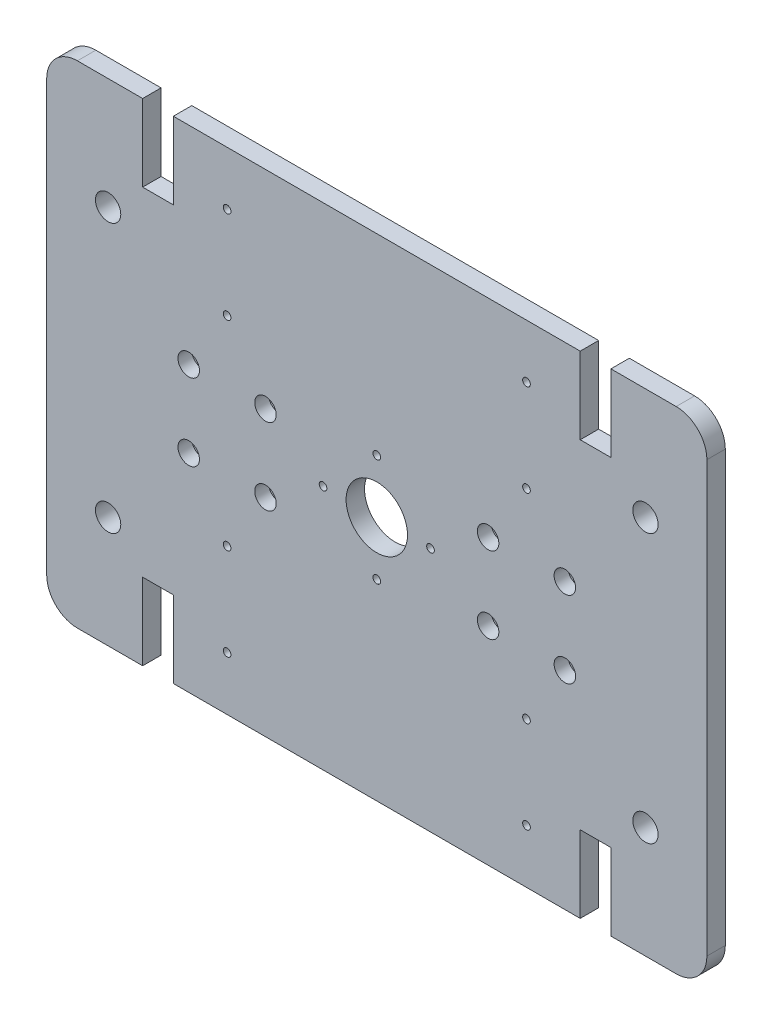
SolidWorks part; units mm, degrees
material "A3钢"
ref_plane "前视基准面" through (0, 0, 0) normal (0, 0, 1) x (1, 0, 0)
ref_plane "上视基准面" through (0, 0, 0) normal (0, 1, 0) x (1, 0, 0)
ref_plane "右视基准面" through (0, 0, 0) normal (1, 0, 0) x (0, 0, -1)
sketch "草图1" plane through (0, 0, 0) normal (0, 0, 1) x (1, 0, 0)
  line L1 (-195, -160) -> (195, -160)
  line L2 (-215, -140) -> (-215, 140)
  line L3 (-195, 160) -> (195, 160)
  line L4 (215, -140) -> (215, 140)
  line L5 (-215, -160) -> (215, 160) construction
  line L6 (-215, 160) -> (215, -160) construction
  arc A0 (-195, -160) -> (-215, -140) centre (-195, -140) cw
  arc A1 (195, -160) -> (215, -140) centre (195, -140) ccw
  arc A2 (195, 160) -> (215, 140) centre (195, 140) cw
  arc A3 (-215, 140) -> (-195, 160) centre (-195, 140) cw
  point P0 (0, 0)
  dimension "D3" = 20
  dimension "D1" = 430
  dimension "D2" = 320
extrude "凸台-拉伸1" add sketch "草图1" along normal mid plane 12
hole_wizard "Ø16.5 (16.5) 直径孔1" positions "草图4" profile "草图6" hole size "Ø16.5" standard "GB" end condition through all
sketch "草图4" plane through (0, 0, 6) normal (0, 0, 1) x (1, 0, 0)
  line L0 (-231.3425, 0) -> (233.1499, 0) construction
  line L3 (0, 185.8572) -> (0, -190.0744) construction
  point P0 (-175, 87.5)
  point P20 (175, 87.5)
  point P21 (175, -87.5)
  point P22 (-175, -87.5)
  dimension "D1" = 350
  dimension "D2" = 175
sketch "草图6" plane through (-175, 87.5, 6) normal (1, 0, 0) x (0, -1, 0)
  line L0 (0, 0) -> (0, 12)
  line L1 (0, 12) -> (8.25, 12)
  line L2 (8.25, 12) -> (8.25, 0)
  line L5 (8.25, 0) -> (0, 0)
  line L11 (0, -6.35) -> (0, 107.95) construction
  dimension "通孔孔直径" = 16.5
  dimension "通孔孔深度" = 12
sketch "草图11" plane through (0, 0, 6) normal (0, 0, 1) x (1, 0, 0)
  circle A0 centre (0, 0) radius 20
  dimension "D1" = 40
extrude "切除-拉伸1" cut sketch "草图11" against normal through all
hole_wizard "打孔尺寸(%根据)内六角圆柱头螺钉的类型2" positions "草图12" profile "草图14" counterbore size "M8" standard "GB" end condition through all
sketch "草图12" plane through (0, 0, 6) normal (0, 0, 1) x (1, 0, 0)
  line L1 (-122.5, 25) -> (-72.5, 25) construction
  line L2 (-122.5, 25) -> (-122.5, -25) construction
  line L3 (-122.5, -25) -> (-72.5, -25) construction
  line L4 (-72.5, 25) -> (-72.5, -25) construction
  line L5 (233.5009, 0) -> (-225.4099, 0) construction
  line L8 (0, -164.2167) -> (0, 163.8346) construction
  point P0 (-122.5, 25)
  point P3 (-72.5, 25)
  point P7 (-72.5, -25)
  point P72 (-122.5, -25)
  point P96 (72.5, -25)
  point P97 (122.5, -25)
  point P98 (72.5, 25)
  point P99 (122.5, 25)
  dimension "D1" = 50
  dimension "D2" = 50
  dimension "D3" = 145
sketch "草图14" plane through (-122.5, 25, 6) normal (1, 0, 0) x (0, -1, 0)
  line L0 (0, 0) -> (0, 12)
  line L1 (0, 12) -> (4.5, 12)
  line L3 (4.5, 12) -> (4.5, 9)
  line L4 (4.5, 9) -> (7, 9)
  line L5 (7, 9) -> (7, 0)
  line L7 (7, 0) -> (0, 0)
  line L11 (0, -6.35) -> (0, 107.95) construction
  dimension "通孔孔直径" = 9
  dimension "通孔孔深度" = 12
  dimension "柱形沉头孔直径" = 14
  dimension "柱形沉头孔深度" = 9
hole_wizard "M6 螺纹孔1" positions "草图15" profile "草图16" tap size "M6" standard "GB" end condition through all
sketch "草图15" plane through (0, 0, -6) normal (0, 0, -1) x (-1, 0, 0)
  line L2 (-234.5636, 0) -> (248.1873, 0) construction
  line L5 (0, 162.0029) -> (0, -158.4489) construction
  point P0 (-97.5, 65)
  point P2 (-97.5, 125)
  point P22 (-97.5, -125)
  point P23 (-97.5, -65)
  point P24 (97.5, -65)
  point P25 (97.5, -125)
  point P26 (97.5, 125)
  point P27 (97.5, 65)
  dimension "D1" = 195
  dimension "D2" = 130
  dimension "D3" = 60
sketch "草图16" plane through (97.5, 65, -6) normal (1, 0, 0) x (0, 1, 0)
  line L0 (0, 0) -> (0, 12)
  line L1 (0, 12) -> (2.5, 12)
  line L2 (2.5, 12) -> (2.5, 0)
  line L5 (2.5, 0) -> (0, 0)
  line L11 (0, -6.35) -> (0, 107.95) construction
  dimension "通孔螺纹孔钻头直径" = 5
  dimension "通孔螺纹孔钻头深度" = 12
cosmetic thread "孔螺蚊线5" parameters "D2"=6
cosmetic thread "孔螺蚊线6" parameters "D2"=6
cosmetic thread "孔螺蚊线7" parameters "D2"=6
cosmetic thread "孔螺蚊线8" parameters "D2"=6
cosmetic thread "孔螺蚊线9" parameters "D2"=6
cosmetic thread "孔螺蚊线10" parameters "D2"=6
cosmetic thread "孔螺蚊线11" parameters "D2"=6
cosmetic thread "孔螺蚊线12" parameters "D2"=6
sketch "草图17" plane through (0, 0, 6) normal (0, 0, 1) x (1, 0, 0)
  line L0 (195, 160) -> (-195, 160) construction
  line L1 (-152.5, 160) -> (-132.5, 160)
  line L2 (-152.5, 160) -> (-152.5, 110)
  line L3 (-152.5, 110) -> (-132.5, 110)
  line L4 (-132.5, 160) -> (-132.5, 110)
  line L5 (-237.7667, 0) -> (231.7926, 0) construction
  line L6 (0, 163.9873) -> (0, -179.5198) construction
  line L7 (132.5, 160) -> (132.5, 110)
  line L8 (152.5, 110) -> (132.5, 110)
  line L9 (152.5, 160) -> (152.5, 110)
  line L10 (152.5, 160) -> (132.5, 160)
  line L11 (152.5, -160) -> (132.5, -160)
  line L12 (152.5, -160) -> (152.5, -110)
  line L13 (152.5, -110) -> (132.5, -110)
  line L14 (132.5, -160) -> (132.5, -110)
  line L15 (-132.5, -160) -> (-132.5, -110)
  line L16 (-152.5, -110) -> (-132.5, -110)
  line L17 (-152.5, -160) -> (-152.5, -110)
  line L18 (-152.5, -160) -> (-132.5, -160)
  point P23 (-142.5, 110)
  point P24 (142.5, 110)
  dimension "D1" = 285
  dimension "D2" = 20
  dimension "D3" = 50
extrude "切除-拉伸2" cut sketch "草图17" against normal through all
sketch "草图18" plane through (0, 0, 6) normal (0, 0, 1) x (1, 0, 0)
  line L0 (0, 0) -> (0, 106.199) construction
  circle A0 centre (0, 0) radius 35
  dimension "D1" = 70
hole_wizard "M6 螺纹孔2" positions "3D草图1" profile "草图20" tap size "M6" standard "GB" end condition through all
sketch3d "3D草图1"
  line L0 (0, 0, 6) -> (0, 106.199, 6) construction
  circle A0 centre (0, 0, 6) radius 35 construction
  point P0 (0, 35, 6)
  point P4 (0, 0, 41)
sketch "草图20" plane through (0, 35, 6) normal (1, 0, 0) x (0, -1, 0)
  line L0 (0, 0) -> (0, 12)
  line L1 (0, 12) -> (2.5, 12)
  line L2 (2.5, 12) -> (2.5, 0)
  line L5 (2.5, 0) -> (0, 0)
  line L11 (0, -6.35) -> (0, 107.95) construction
  dimension "通孔螺纹孔钻头直径" = 5
  dimension "通孔螺纹孔钻头深度" = 12
cosmetic thread "孔螺蚊线13" parameters "D2"=6
pattern_circular "阵列(圆周)1" count 4 over 360 about axis through (0, 0, 0) along (0, 0, 1) of "M6 螺纹孔2"
